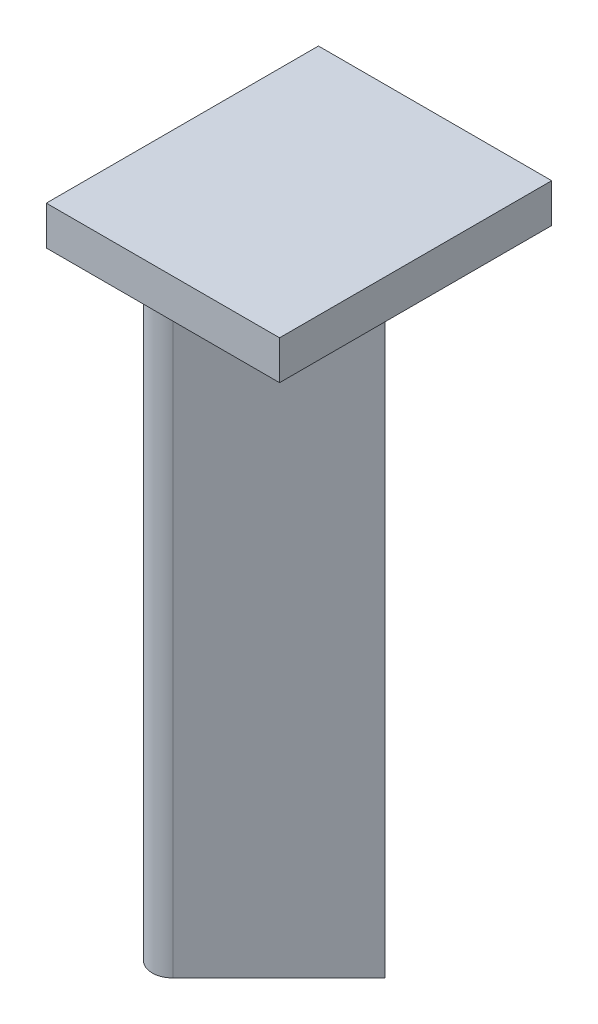
SolidWorks part; units mm, degrees
ref_plane "Front Plane" through (0, 0, 0) normal (0, 0, 1) x (1, 0, 0)
ref_plane "Top Plane" through (0, 0, 0) normal (0, 1, 0) x (1, 0, 0)
ref_plane "Right Plane" through (0, 0, 0) normal (1, 0, 0) x (0, 0, -1)
sketch "Sketch1" plane through (0, 0, 0) normal (0, 1, 0) x (1, 0, 0)
  line L0 (-9.8288, 9.8288) -> (-0.7071, 0.7071) construction
  line L1 (-0.7071, -0.7071) -> (-9.8288, -9.8288) construction
  line L2 (-6.0104, 13.6472) -> (7.6368, 0) construction
  line L3 (7.6368, 0) -> (-6.0104, -13.6472) construction
  line L4 (-6.0245, 13.633) -> (7.6085, 0)
  line L5 (-9.8288, 9.8288) -> (0, 0) construction
  line L6 (0, 0) -> (-9.8288, -9.8288) construction
  line L7 (7.6085, 0) -> (-6.0245, -13.633)
  line L8 (-0.707, -0.7353) -> (-9.8146, -9.8429)
  line L9 (-9.8146, 9.8429) -> (-0.707, 0.7353)
  line L10 (0, 0) -> (7.6368, 0) construction
  arc A0 (-9.8288, 9.8288) -> (-6.0104, 13.6472) centre (-7.9196, 11.738) cw construction
  arc A1 (-6.0104, -13.6472) -> (-9.8288, -9.8288) centre (-7.9196, -11.738) cw construction
  arc A2 (-0.7071, -0.7071) -> (-0.7071, 0.7071) centre (0, 0) ccw construction
  arc A3 (-6.0245, -13.633) -> (-9.8146, -9.8429) centre (-7.9196, -11.738) cw
  arc A4 (-0.707, -0.7353) -> (-0.707, 0.7353) centre (0, 0) ccw
  arc A5 (-9.8146, 9.8429) -> (-6.0245, 13.633) centre (-7.9196, 11.738) cw
  dimension "D4" = 0.02
  dimension "D2" = 19.3
  dimension "D3" = 19.3
  dimension "D1" = 5.4
extrude "Boss-Extrude1" add sketch "Sketch1" along normal blind 78
sketch "Sketch2" plane through (0, 78, 0) normal (0, 1, 0) x (1, 0, 0)
  line L1 (-17.4793, -18.4751) -> (12.5207, -18.4751)
  line L2 (-17.4793, -18.4751) -> (-17.4793, 16.5249)
  line L3 (-17.4793, 16.5249) -> (12.5207, 16.5249)
  line L4 (12.5207, -18.4751) -> (12.5207, 16.5249)
extrude "Boss-Extrude2" add sketch "Sketch2" along normal blind 5 contours L2 L3 L4 L1
